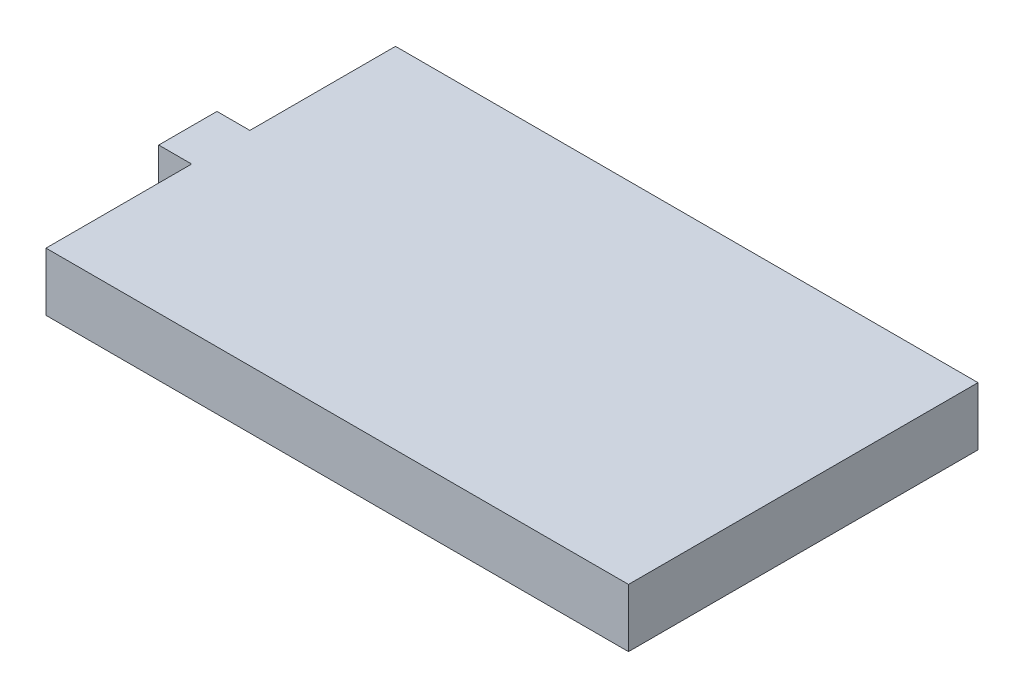
SolidWorks part; units mm, degrees
ref_plane "Front Plane" through (0, 0, 0) normal (0, 0, 1) x (1, 0, 0)
ref_plane "Top Plane" through (0, 0, 0) normal (0, 1, 0) x (1, 0, 0)
ref_plane "Right Plane" through (0, 0, 0) normal (1, 0, 0) x (0, 0, -1)
sketch "Sketch1" plane through (0, 0, 0) normal (0, 1, 0) x (1, 0, 0)
  line L0 (-31.75, 3.175) -> (-31.75, 19.05)
  line L1 (31.75, -19.05) -> (-31.75, -19.05)
  line L2 (31.75, -19.05) -> (31.75, 19.05)
  line L3 (31.75, 19.05) -> (-31.75, 19.05)
  line L4 (-31.75, -19.05) -> (-31.75, -3.175)
  line L5 (31.75, -19.05) -> (-31.75, 19.05) construction
  line L6 (31.75, 19.05) -> (-31.75, -19.05) construction
  line L7 (-31.75, -3.175) -> (-35.3379, -3.175)
  line L9 (-31.75, 3.175) -> (-35.3379, 3.175)
  line L10 (-35.3379, -3.175) -> (-35.3379, 3.175)
  line L11 (-35.3379, 0) -> (-27.4822, 0) construction
  line L12 (31.75, 0) -> (-19.737, 0) construction
  point P0 (0, 0)
  point P6 (-25.4, 0)
  dimension "D1" = 63.5
  dimension "D2" = 38.1
  dimension "D3" = 0
  dimension "D4" = 6.35
extrude "Boss-Extrude1" add sketch "Sketch1" along normal blind 6.35
